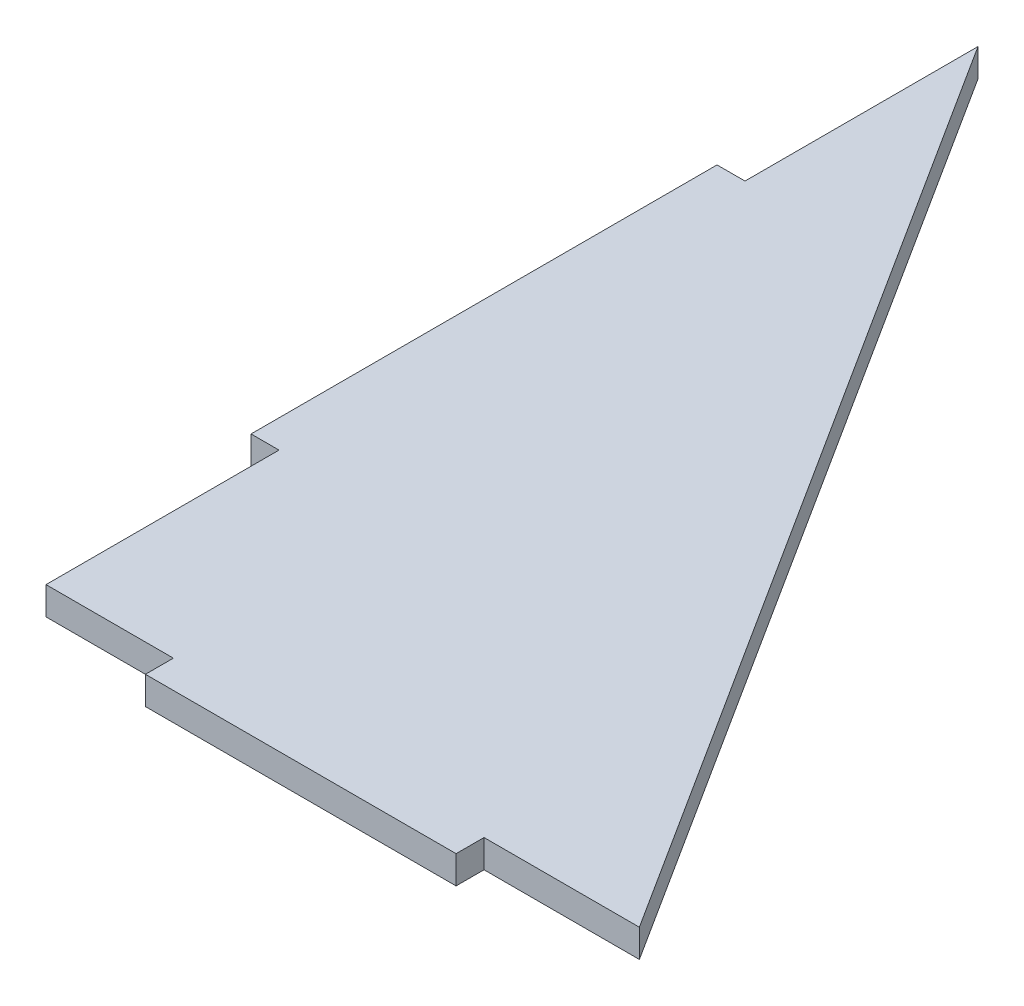
SolidWorks part; units mm, degrees
ref_plane "Front Plane" through (0, 0, 0) normal (0, 0, 1) x (1, 0, 0)
ref_plane "Top Plane" through (0, 0, 0) normal (0, 1, 0) x (1, 0, 0)
ref_plane "Right Plane" through (0, 0, 0) normal (1, 0, 0) x (0, 0, -1)
sketch "Sketch1" plane through (0, 0, 0) normal (0, 1, 0) x (1, 0, 0)
  line L0 (0, 0) -> (95.5, 0)
  line L1 (-55, 0) -> (55, 0) construction
  line L2 (0, 0) -> (0, 150)
  line L3 (0, -55) -> (0, 55) construction
  line L4 (0, 150) -> (95.5, 0)
  line L6 (20.5, 4.5) -> (70.5, 4.5)
  line L7 (20.5, 4.5) -> (20.5, -4.5)
  line L8 (20.5, -4.5) -> (70.5, -4.5)
  line L9 (70.5, 4.5) -> (70.5, -4.5)
  line L10 (20.5, 4.5) -> (70.5, -4.5) construction
  line L11 (20.5, -4.5) -> (70.5, 4.5) construction
  line L12 (-4.5, 112.5) -> (4.5, 112.5)
  line L13 (-4.5, 112.5) -> (-4.5, 37.5)
  line L14 (-4.5, 37.5) -> (4.5, 37.5)
  line L15 (4.5, 112.5) -> (4.5, 37.5)
  line L16 (-4.5, 112.5) -> (4.5, 37.5) construction
  line L17 (-4.5, 37.5) -> (4.5, 112.5) construction
  point P5 (45.5, 0)
  point P13 (0, 75)
  dimension "D1" = 150
  dimension "D2" = 95.5
  dimension "D3" = 9
  dimension "D4" = 50
  dimension "D5" = 20.5
  dimension "D6" = 9
  dimension "D7" = 75
  dimension "D8" = 37.5
extrude "Boss-Extrude1" add sketch "Sketch1" along normal blind 4.5 contours L13 L14 L2 L12 | L12 L15 L14 L2 L0 L7 L6 L9 L4 | L9 L0 L7 L8 | L9 L6 L7 L0 | L15 L12 L2 L14
